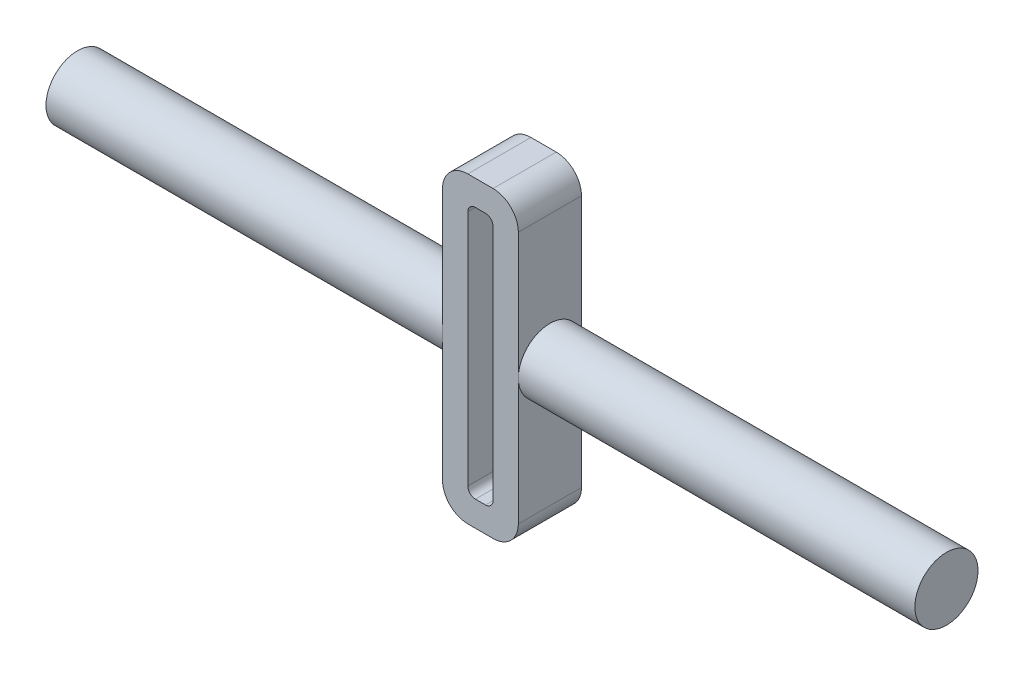
SolidWorks part; units mm, degrees
ref_plane "Front Plane" through (0, 0, 0) normal (0, 0, 1) x (1, 0, 0)
ref_plane "Top Plane" through (0, 0, 0) normal (0, 1, 0) x (1, 0, 0)
ref_plane "Right Plane" through (0, 0, 0) normal (1, 0, 0) x (0, 0, -1)
ref_plane "Plane1" through (0, 0, 25) normal (0, 0, 1) x (1, 0, 0)
sketch "Sketch1" plane through (0, 0, 25) normal (0, 0, 1) x (1, 0, 0)
  line L0 (-15, -60) -> (15, -60)
  line L1 (15, -60) -> (15, 60)
  line L2 (15, 60) -> (-15, 60)
  line L3 (-15, 60) -> (-15, -60)
extrude "Boss-Extrude1" add sketch "Sketch1" against normal blind 25
sketch "Sketch2" plane through (0, 0, 0) normal (0, 0, -1) x (-1, 0, 0)
  line L0 (5, -50) -> (5, 50)
  line L1 (5, 50) -> (-5, 50)
  line L2 (-5, 50) -> (-5, -50)
  line L3 (-5, -50) -> (5, -50)
extrude "Cut-Extrude1" cut sketch "Sketch2" against normal through all
ref_plane "Plane2" through (0, 0, 12.5) normal (0, 0, 1) x (1, 0, 0)
sketch "Sketch3" plane through (0, 0, 12.5) normal (0, 0, 1) x (1, 0, 0)
  line L0 (-175, 12.5) -> (-175, 0)
  line L1 (-175, 0) -> (-15, 0)
  line L2 (-15, 0) -> (-15, 12.5)
  line L3 (-15, 12.5) -> (-175, 12.5)
  line L4 (-175, 0) -> (-15, 0) construction
revolve "Revolve1" add sketch "Sketch3" angle 360 about L4
ref_plane "Plane3" through (0, 0, 12.5) normal (0, 0, -1) x (-1, 0, 0)
sketch "Sketch4" plane through (0, 0, 12.5) normal (0, 0, -1) x (-1, 0, 0)
  line L0 (-175, 12.5) -> (-175, 0)
  line L1 (-175, 0) -> (-15, 0)
  line L2 (-15, 0) -> (-15, 12.5)
  line L3 (-15, 12.5) -> (-175, 12.5)
  line L4 (-175, 0) -> (-15, 0) construction
revolve "Revolve2" add sketch "Sketch4" angle 360 about L4
fillet "Fillet1" radius 3 4 edges at (-5, -50, 12.5) (-5, 50, 12.5) (5, -50, 12.5) (5, 50, 12.5)
fillet "Fillet2" radius 10 4 edges at (15, -60, 12.5) (-15, 60, 12.5) (15, 60, 12.5) (-15, -60, 12.5)
sketch "Sketch5" plane through (175, 0, 0) normal (1, 0, 0) x (0, 0, -1)
  circle A2 centre (-12.5, 0) radius 12.5
  circle A3 centre (-12.5, 0) radius 12.5
  dimension "D1" = 0
extrude "Cut-Extrude2" cut sketch "Sketch5" against normal blind 3
sketch "Sketch6" plane through (-175, 0, 0) normal (-1, 0, 0) x (0, 0, 1)
  circle A1 centre (12.5, 0) radius 12.5
  circle A2 centre (12.5, 0) radius 12.5
  dimension "D1" = 0
extrude "Cut-Extrude3" cut sketch "Sketch6" against normal blind 3
